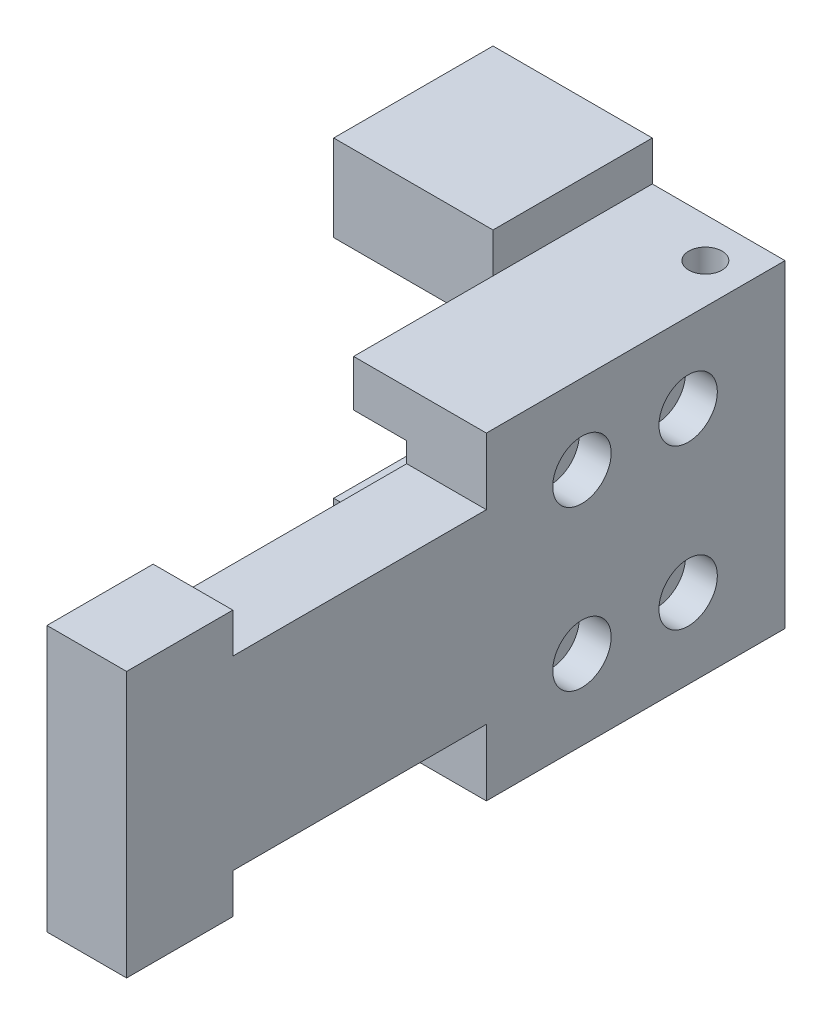
SolidWorks part; units mm, degrees
ref_plane "前视基准面" through (0, 0, 0) normal (0, 0, 1) x (1, 0, 0)
ref_plane "上视基准面" through (0, 0, 0) normal (0, 1, 0) x (1, 0, 0)
ref_plane "右视基准面" through (0, 0, 0) normal (1, 0, 0) x (0, 0, -1)
sketch "草图1" plane through (0, 0, 0) normal (0, 0, 1) x (1, 0, 0)
  line L0 (-6, 8.5) -> (-6, -8.5)
  line L1 (0, -10) -> (0, 10)
  line L5 (-10, 12) -> (0, 12)
  line L6 (-6, 8.5) -> (-10, 8.5)
  line L7 (0, 10) -> (0, 12)
  line L8 (-10, -8.5) -> (-6, -8.5)
  line L9 (-10, -12) -> (0, -12)
  line L11 (0, -10) -> (0, -12)
  line L12 (-22, 15) -> (-10, 15)
  line L13 (-10, 15) -> (-10, 12)
  line L14 (-22, 8.5) -> (-22, 15)
  line L15 (-22, 8.5) -> (-10, 8.5)
  line L16 (-22, -15) -> (-22, -8.5)
  line L17 (-10, -15) -> (-22, -15)
  line L18 (-10, -15) -> (-10, -12)
  line L19 (-22, -8.5) -> (-10, -8.5)
  line L40 (-30.9359, 0) -> (8.6402, 0) construction
  line L41 (-19.805, 11.75) -> (-14.195, 11.75) construction
  line L42 (-17, 8.945) -> (-17, 14.555) construction
  line L43 (-19.805, -11.75) -> (-14.195, -11.75) construction
  line L44 (-17, -14.555) -> (-17, -8.945) construction
  circle A0 centre (-17, 11.75) radius 2.55 construction
  circle A1 centre (-9300.7431, 125.8312) radius 2.55 construction
extrude "凸台-拉伸1" add sketch "草图1" along normal blind 49.6
sketch "草图2" plane through (0, -15, 0) normal (0, -1, 0) x (1, 0, 0)
  line L0 (-10, 49.6) -> (0, 49.6) construction
  line L1 (-22, 49.6) -> (-12.9551, 49.6)
  line L2 (-22, 49.6) -> (-22, 12)
  line L3 (-22, 12) -> (-10, 12)
  line L4 (-10, 22.5) -> (-10, 12)
  line L5 (-10, 22.5) -> (-6, 22.5)
  line L6 (-22, 0) -> (-10, 0) construction
  line L7 (-12.9551, 49.6) -> (-6, 49.6)
  line L8 (-6, 22.5) -> (-6, 49.6)
  line L9 (-10, 0) -> (0, 0) construction
  line L10 (0, 49.6) -> (0, 0) construction
  point P10 (-16, 12)
  dimension "D1" = 12
  dimension "D2" = 22.5
  dimension "D3" = 10
  dimension "D4" = 6
extrude "切除-拉伸1" cut sketch "草图2" against normal through all
sketch "草图3" plane through (0, 0, 0) normal (1, 0, 0) x (0, 0, -1)
  line L0 (-49.6, 0) -> (9.3592, 0) construction
  line L1 (-49.6, -12) -> (-49.6, 12) construction
  line L2 (-49.6, 12) -> (0, 12) construction
  line L3 (-22.5, 12) -> (-41.6, 12)
  line L4 (-22.5, 12) -> (-22.5, 7)
  line L5 (-22.5, 7) -> (-41.6, 7)
  line L6 (-41.6, 10) -> (-41.6, 7)
  line L7 (0, -12) -> (0, 12) construction
  line L8 (-41.6, 12) -> (-49.6, 12)
  line L9 (-41.6, -12) -> (-49.6, -12)
  line L10 (-41.6, 10) -> (-49.6, 10)
  line L11 (-49.6, 12) -> (-49.6, 10)
  line L12 (-49.6, -12) -> (-49.6, -10)
  line L13 (-41.6, -10) -> (-41.6, -7)
  line L14 (-22.5, -12) -> (-22.5, -7)
  line L15 (-22.5, -7) -> (-41.6, -7)
  line L16 (-41.6, -10) -> (-49.6, -10)
  line L17 (-22.5, -12) -> (-41.6, -12)
  dimension "D1" = 22.5
  dimension "D2" = 41.6
  dimension "D3" = 7
  dimension "D4" = 10
extrude "切除-拉伸2" cut sketch "草图3" against normal blind 49.6
hole_wizard "M2 六角凹头螺钉的柱形沉头孔1" positions "草图4" profile "草图5" counterbore size "M2" standard "ISO"
sketch "草图4" plane through (0, 0, 0) normal (1, 0, 0) x (0, 0, -1)
  line L0 (0, 0) -> (-53.9421, 0) construction
  line L2 (0, -12) -> (0, 12) construction
  point P0 (-15.3, 6)
  point P2 (-7.3, 6)
  point P4 (-15.3, -6)
  point P6 (-7.3, -6)
  point P14 (0, 0)
  dimension "D1" = 12
  dimension "D2" = 7.3
  dimension "D3" = 15.3
sketch "草图5" plane through (0, 6, 15.3) normal (0, 1, 0) x (0, 0, -1)
  line L0 (0, 0) -> (0, 10.821)
  line L1 (0, 10.821) -> (1.2, 10.1)
  line L2 (1.2, 10.1) -> (1.2, 2.4)
  line L3 (1.2, 2.4) -> (2.2, 2.4)
  line L4 (2.2, 2.4) -> (2.2, 0)
  line L5 (2.2, 0) -> (0, 0)
  line L10 (0, 10.821) -> (-1.2, 10.1) construction
  line L11 (0, -6.35) -> (0, 107.95) construction
  dimension "孔直径" = 2.4
  dimension "孔深度" = 10.1
  dimension "柱形沉头孔直径" = 4.4
  dimension "柱形沉头孔深度" = 2.4
  dimension "导头角度" = 118
sketch "草图6" plane through (0, 0, 0) normal (0, 0, -1) x (-1, 0, 0)
  line L0 (0, 0) -> (32.508, 0) construction
  line L1 (0, -12) -> (0, 12) construction
  circle A0 centre (17, -11.75) radius 2.55
  circle A1 centre (17, 11.75) radius 2.55
  dimension "D1" = 5.1
  dimension "D2" = 23.5
  dimension "D3" = 17
extrude "切除-拉伸3" cut sketch "草图6" against normal blind 6
hole_wizard "M3 螺纹孔1" positions "草图7" profile "草图8" tap size "M3" standard "ISO"
sketch "草图7" plane through (0, 12, 0) normal (0, 1, 0) x (1, 0, 0)
  line L1 (0, -22.5) -> (0, 0) construction
  line L2 (0, 0) -> (-10, 0) construction
  point P0 (-3, -3)
  dimension "D1" = 3
  dimension "D2" = 3
sketch "草图8" plane through (-3, 12, 3) normal (1, 0, 0) x (0, 0, 1)
  line L0 (0, 0) -> (0, 8.2511)
  line L1 (0, 8.2511) -> (1.25, 7.5)
  line L2 (1.25, 7.5) -> (1.25, 0)
  line L5 (1.25, 0) -> (0, 0)
  line L10 (0, 8.2511) -> (-1.25, 7.5) construction
  line L11 (0, -6.35) -> (0, 107.95) construction
  dimension "螺纹孔钻头直径" = 2.5
  dimension "螺纹孔钻头深度" = 7.5
  dimension "导头角度" = 118
cosmetic thread "孔螺蚊线1" parameters "D1"=6, "D2"=3
